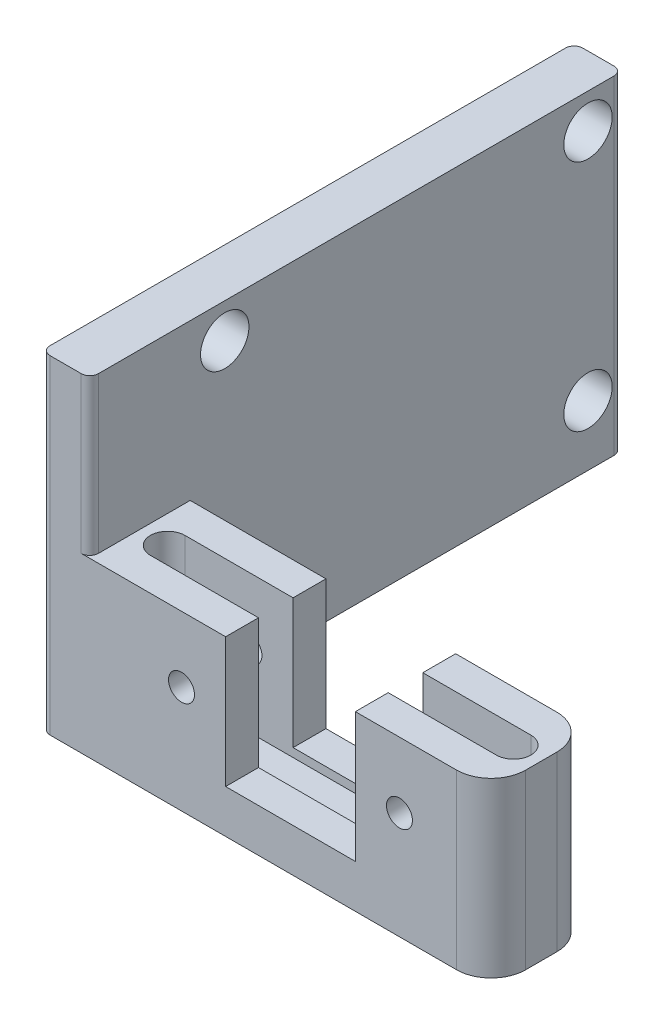
SolidWorks part; units mm, degrees
ref_plane "前视" through (0, 0, 0) normal (0, 0, 1) x (1, 0, 0)
ref_plane "上视" through (0, 0, 0) normal (0, 1, 0) x (1, 0, 0)
ref_plane "右视" through (0, 0, 0) normal (1, 0, 0) x (0, 0, -1)
sketch "草图1" plane through (0, 0, 0) normal (0, 1, 0) x (1, 0, 0)
  line L0 (-5.22, 18.4025) -> (-2.42, 18.4025)
  line L1 (-2.42, 18.4025) -> (-2.42, -6.5975)
  line L2 (-2.42, -6.5975) -> (20.78, -6.5975)
  line L3 (20.78, -6.5975) -> (20.78, -12.3975)
  line L4 (20.78, -12.3975) -> (-5.22, -12.3975)
  line L5 (-5.22, -12.3975) -> (-5.22, 18.4025)
  dimension "D1" = 5.8
  dimension "D2" = 26
  dimension "D3" = 30.8
  dimension "D4" = 2.8
extrude "凸台-拉伸1" add sketch "草图1" along normal blind 19
sketch "草图3" plane through (0, 0, 12.3975) normal (0, 0, 1) x (1, 0, 0)
  line L2 (20.78, 19) -> (-2.42, 19)
  line L3 (20.78, 19) -> (20.78, 10)
  line L5 (20.78, 10) -> (-2.42, 10)
  line L6 (-2.42, 19) -> (-2.42, 10)
  dimension "D1" = 23.2
  dimension "D2" = 9
extrude "切除-拉伸2" cut sketch "草图3" against normal through all
sketch "草图4" plane through (0, 10, 0) normal (0, 1, 0) x (1, 0, 0)
  line L0 (3.6992, -9.4975) -> (13.842, -9.4975) construction
  line L2 (-2.42, -6.5975) -> (20.78, -6.5975) construction
  line L3 (9.18, -7.9821) -> (9.18, -10.8799) construction
  line L4 (20.78, -6.5975) -> (20.78, -12.3975) construction
  line L5 (-0.82, -9.4975) -> (19.18, -9.4975) construction
  line L6 (-0.82, -8.4975) -> (19.18, -8.4975)
  line L7 (-0.82, -10.4975) -> (19.18, -10.4975)
  arc A0 (-0.82, -8.4975) -> (-0.82, -10.4975) centre (-0.82, -9.4975) ccw
  arc A1 (19.18, -10.4975) -> (19.18, -8.4975) centre (19.18, -9.4975) ccw
  point P10 (9.18, -9.4975)
  dimension "D2" = 11.6
  dimension "D1" = 2.9
extrude "切除-拉伸3" cut sketch "草图4" against normal blind 8
sketch "草图5" plane through (0, 0, 12.3975) normal (0, 0, 1) x (1, 0, 0)
  line L0 (-2.42, 10) -> (20.78, 10) construction
  line L1 (12.93, 2.5) -> (5.43, 2.5)
  line L2 (12.93, 2.5) -> (12.93, 10)
  line L3 (12.93, 10) -> (5.43, 10)
  line L4 (5.43, 2.5) -> (5.43, 10)
  line L5 (12.93, 2.5) -> (5.43, 10) construction
  line L6 (12.93, 10) -> (5.43, 2.5) construction
  line L7 (20.78, 10) -> (20.78, 0) construction
  point P0 (9.18, 6.25)
  dimension "D1" = 7.5
  dimension "D2" = 11.6
  dimension "D3" = 7.5
extrude "切除-拉伸4" cut sketch "草图5" against normal through all
sketch "草图6" plane through (-5.22, 0, 0) normal (-1, 0, 0) x (0, 0, 1)
  line L0 (-18.4025, 19) -> (12.3975, 19) construction
  line L1 (-18.4025, 19) -> (-18.4025, 0) construction
  circle A0 centre (-16.4025, 17) radius 1.4
  circle A1 centre (4.5975, 17) radius 1.4
  circle A2 centre (-16.4025, 3.5) radius 1.4
  circle A3 centre (4.5975, 3.5) radius 1.4
  dimension "D1" = 2
  dimension "D2" = 2
  dimension "D3" = 2
  dimension "D4" = 13.5
  dimension "D5" = 21
  dimension "D6" = 21
  dimension "D7" = 2
  dimension "D8" = 13.5
extrude "切除-拉伸5" cut sketch "草图6" against normal through all
sketch "草图7" plane through (0, 0, 12.3975) normal (0, 0, 1) x (1, 0, 0)
  line L0 (5.43, 10) -> (5.43, 2.5) construction
  line L1 (12.93, 2.5) -> (12.93, 10) construction
  line L2 (-2.42, 10) -> (5.43, 10) construction
  line L3 (12.93, 10) -> (20.78, 10) construction
  circle A0 centre (2.88, 6.2) radius 0.75
  circle A1 centre (15.48, 6.2) radius 0.75
  point P6 (12.93, 6.25)
  dimension "D1" = 1.5
  dimension "D2" = 1.5
  dimension "D3" = 2.55
  dimension "D4" = 2.55
  dimension "D5" = 3.8
  dimension "D6" = 3.8
extrude "切除-拉伸6" cut sketch "草图7" against normal through all
fillet "圆角2" radius 0.5 3 edges at (-2.42, 9.5, -18.4025) (-5.22, 9.5, -18.4025) (-5.22, 9.5, 12.3975)
fillet "圆角3" radius 2 2 edges at (20.78, 5, 12.3975) (20.78, 5, 6.5975)
fillet "圆角4" radius 0.5 1 edges at (-2.42, 14.5, 12.3975)
